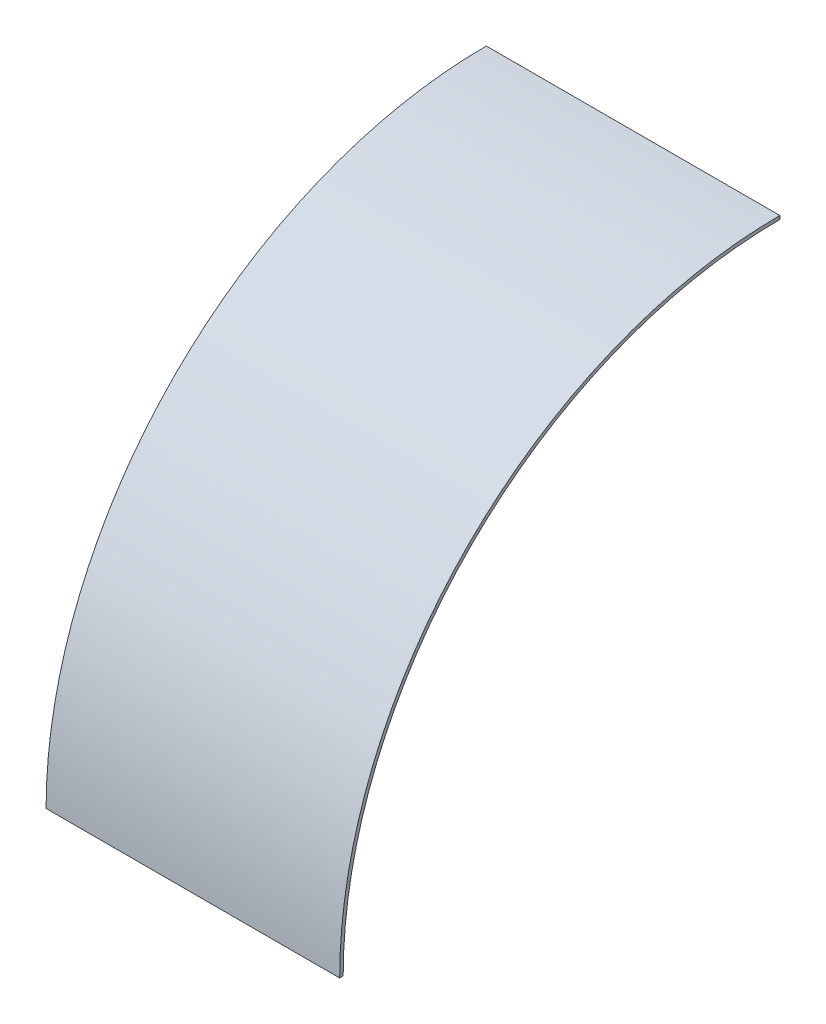
SolidWorks part; units mm, degrees
ref_plane "Front Plane" through (0, 0, 0) normal (0, 0, 1) x (1, 0, 0)
ref_plane "Top Plane" through (0, 0, 0) normal (0, 1, 0) x (1, 0, 0)
ref_plane "Right Plane" through (0, 0, 0) normal (1, 0, 0) x (0, 0, -1)
sketch "Sketch1" plane through (0, 0, 0) normal (1, 0, 0) x (0, 0, -1)
  arc A0 (0, 198.374) -> (-198.374, 0) centre (0, 0) ccw
  dimension "D1" = 198.374
extrude "Extrude-Thin1" add sketch "Sketch1" along normal blind 133.35 thin
